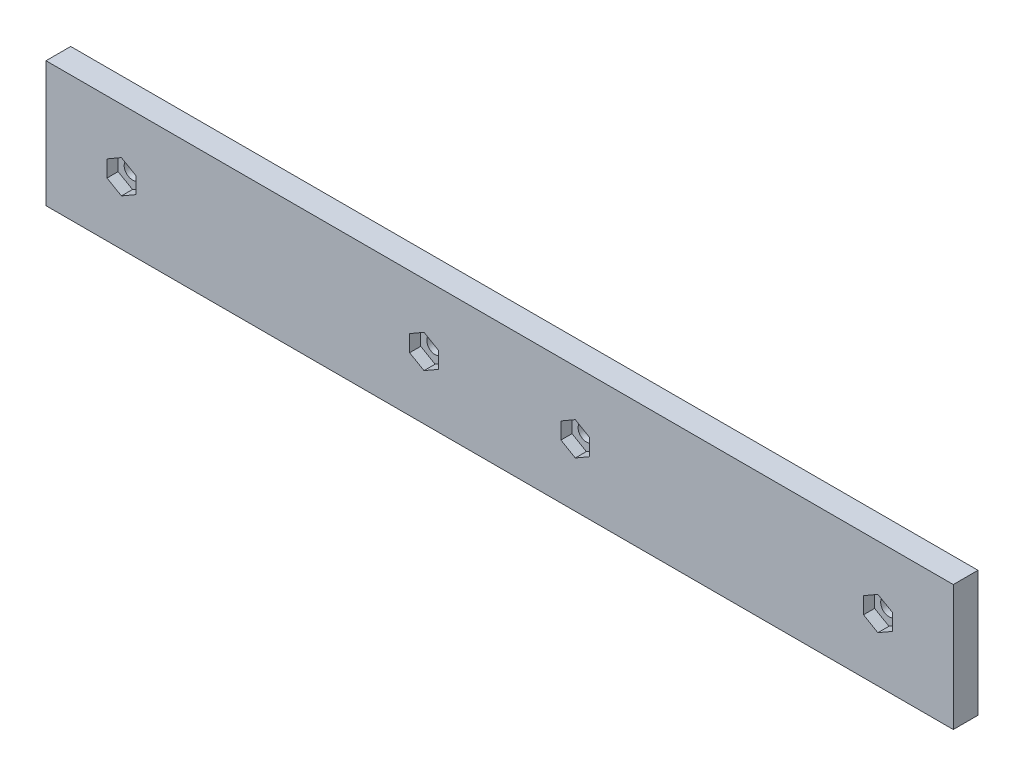
SolidWorks part; units mm, degrees
material "ABS"
ref_plane "Front Plane" through (0, 0, 0) normal (0, 0, 1) x (1, 0, 0)
ref_plane "Top Plane" through (0, 0, 0) normal (0, 1, 0) x (1, 0, 0)
ref_plane "Right Plane" through (0, 0, 0) normal (1, 0, 0) x (0, 0, -1)
sketch "Sketch1" plane through (0, 0, 0) normal (0, 0, 1) x (1, 0, 0)
  line L0 (-779.0929, 5.23) -> (49220.9071, 5.23) construction
  line L1 (220.9071, 17.73) -> (220.9071, -7.27) construction
  line L2 (130.9071, -994.77) -> (130.9071, 49005.23) construction
  line L3 (130.9071, -7.27) -> (130.9071, 17.73) construction
  line L6 (220.8571, -7.22) -> (40.9571, -7.22)
  line L7 (220.8571, -7.22) -> (220.8571, 17.68)
  line L8 (220.8571, 17.68) -> (40.9571, 17.68)
  line L9 (40.9571, -7.22) -> (40.9571, 17.68)
  line L10 (220.9071, -7.27) -> (130.9071, -7.27) construction
  line L11 (220.9071, 17.73) -> (220.9071, -7.27) construction
  circle A0 centre (205.9071, 5.23) radius 1.65
  circle A1 centre (145.9071, 5.23) radius 1.65
  circle A2 centre (115.9071, 5.23) radius 1.65
  circle A3 centre (55.9071, 5.23) radius 1.65
  circle A5 centre (205.9071, 5.23) radius 1.65 construction
  point P9 (220.9071, 5.23)
  point P15 (130.9071, 5.23)
  dimension "D1" = 0.05
  dimension "D2" = 0.05
extrude "Boss-Extrude1" add sketch "Sketch1" along normal blind 4.9
sketch "Sketch2" plane through (0, 0, 4.9) normal (0, 0, 1) x (1, 0, 0)
  line L1 (58.7571, 3.5846) -> (58.7571, 6.8755)
  line L2 (58.7571, 6.8755) -> (55.9071, 8.5209)
  line L3 (55.9071, 8.5209) -> (53.0571, 6.8755)
  line L4 (53.0571, 6.8755) -> (53.0571, 3.5846)
  line L5 (53.0571, 3.5846) -> (55.9071, 1.9391)
  line L6 (55.9071, 1.9391) -> (58.7571, 3.5846)
  line L7 (118.7571, 3.5846) -> (118.7571, 6.8755)
  line L8 (118.7571, 6.8755) -> (115.9071, 8.5209)
  line L9 (115.9071, 8.5209) -> (113.0571, 6.8755)
  line L10 (113.0571, 6.8755) -> (113.0571, 3.5846)
  line L11 (113.0571, 3.5846) -> (115.9071, 1.9391)
  line L12 (115.9071, 1.9391) -> (118.7571, 3.5846)
  line L13 (148.7571, 3.5846) -> (148.7571, 6.8755)
  line L14 (148.7571, 6.8755) -> (145.9071, 8.5209)
  line L15 (145.9071, 8.5209) -> (143.0571, 6.8755)
  line L16 (143.0571, 6.8755) -> (143.0571, 3.5846)
  line L17 (143.0571, 3.5846) -> (145.9071, 1.9391)
  line L18 (145.9071, 1.9391) -> (148.7571, 3.5846)
  line L19 (208.7571, 3.5846) -> (208.7571, 6.8755)
  line L20 (208.7571, 6.8755) -> (205.9071, 8.5209)
  line L21 (205.9071, 8.5209) -> (203.0571, 6.8755)
  line L22 (203.0571, 6.8755) -> (203.0571, 3.5846)
  line L23 (203.0571, 3.5846) -> (205.9071, 1.9391)
  line L24 (205.9071, 1.9391) -> (208.7571, 3.5846)
  circle A0 centre (55.9071, 5.23) radius 2.85 construction
  circle A1 centre (115.9071, 5.23) radius 2.85 construction
  circle A2 centre (145.9071, 5.23) radius 2.85 construction
  circle A3 centre (205.9071, 5.23) radius 2.85 construction
  dimension "D1" = 5.7
extrude "Cut-Extrude1" cut sketch "Sketch2" against normal blind 2.2
